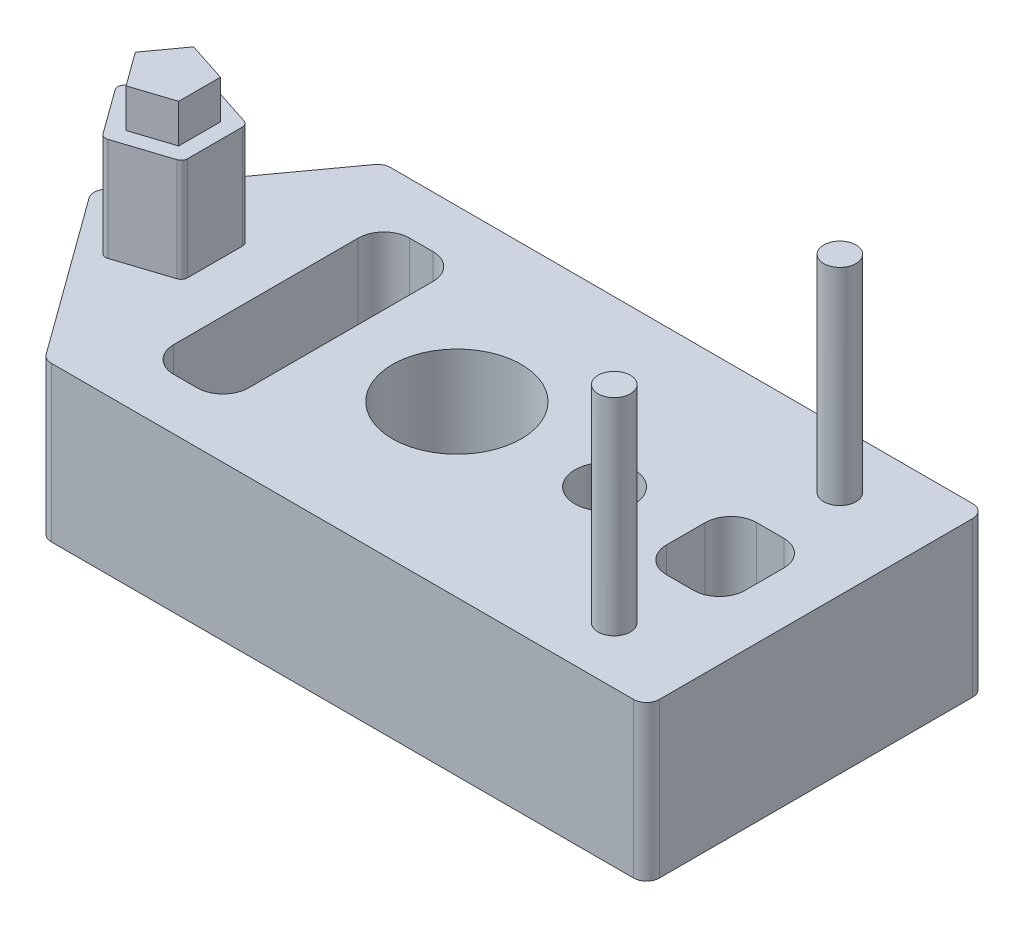
SolidWorks part; units mm, degrees
ref_plane "Front Plane" through (0, 0, 0) normal (0, 0, 1) x (1, 0, 0)
ref_plane "Top Plane" through (0, 0, 0) normal (0, 1, 0) x (1, 0, 0)
ref_plane "Right Plane" through (0, 0, 0) normal (1, 0, 0) x (0, 0, -1)
sketch "Sketch1" plane through (0, 0, 0) normal (0, 1, 0) x (1, 0, 0)
  line L0 (27.85, 13.15) -> (-18.2757, 13.15)
  line L1 (-18.2757, -13.15) -> (27.85, -13.15)
  line L2 (27.85, 13.15) -> (27.85, -13.15)
  line L3 (-11.15, 11.15) -> (25.85, 11.15) construction
  line L4 (-11.15, -11.15) -> (-11.15, 11.15) construction
  line L5 (25.85, 11.15) -> (25.85, -11.15) construction
  line L6 (25.85, -11.15) -> (-11.15, -11.15) construction
  line L7 (-18.2757, 13.15) -> (-18.8138, 13.15)
  line L8 (-25.1875, 0) -> (-23.1146, -2.8532) construction
  line L9 (-23.1146, -2.8532) -> (-19.7604, -1.7634) construction
  line L10 (-19.7604, -1.7634) -> (-19.7604, 1.7634) construction
  line L11 (-19.7604, 1.7634) -> (-23.1146, 2.8532) construction
  line L12 (-23.1146, 2.8532) -> (-25.1875, 0) construction
  line L13 (-18.8138, 13.15) -> (-28.3678, 0)
  line L14 (-18.2757, -13.15) -> (-18.8138, -13.15)
  line L15 (-18.8138, -13.15) -> (-28.3678, 0)
  line L16 (-22.1875, 0) -> (-17.1875, 0) construction
  circle A0 centre (-97.1875, 0) radius 80 construction
  circle A1 centre (-97.1875, 0) radius 81.5625 construction
  circle A2 centre (0, 0) radius 15.625 construction
  circle A4 centre (-22.1875, 0) radius 2.4271 construction
  point P10 (27.85, 0)
  point P14 (-11.15, 0)
  dimension "D1" = 160
  dimension "D2" = 163.125
  dimension "D3" = 31.25
  dimension "D9" = 3
  dimension "D4" = 11.15
  dimension "D5" = 22.3
  dimension "D6" = 37
  dimension "D7" = 2
  dimension "D8" = 2
  dimension "D10" = 5
  dimension "D11" = 5
extrude "Boss-Extrude2" add sketch "Sketch1" against normal blind 12
sketch "Sketch3" plane through (0, 0, 0) normal (0, 1, 0) x (1, 0, 0)
  line L0 (-11.15, 13.15) -> (-11.15, -13.15)
  line L1 (27.85, 13.15) -> (-18.8138, 13.15) construction
  line L2 (-18.8138, -13.15) -> (27.85, -13.15) construction
  circle A0 centre (0, 0) radius 5
  circle A1 centre (11.45, 0) radius 1.9 construction
  circle A2 centre (11.45, 0) radius 2.3
  circle A3 centre (0, 0) radius 2.7 construction
  dimension "D1" = 10
  dimension "D4" = 3.8
  dimension "D5" = 0.4
  dimension "D6" = 5.4
  dimension "D2" = 11.15
  dimension "D3" = 22.6
extrude "Cut-Extrude1" cut sketch "Sketch3" against normal through all contours A0 | A2
sketch "Sketch5" plane through (0, 0, 0) normal (0, 1, 0) x (1, 0, 0)
  line L0 (-11.15, -13.15) -> (-11.15, 13.15) construction
  line L1 (-18.8138, -13.15) -> (27.85, -13.15) construction
  line L2 (27.85, 13.15) -> (-18.8138, 13.15) construction
  line L3 (20.95, 8.75) -> (20.95, -8.75) construction
  circle A0 centre (20.95, -8.75) radius 1.25
  circle A1 centre (20.95, 8.75) radius 1.25
  point P11 (20.95, 0)
  dimension "D4" = 2.5
  dimension "D1" = 11.15
  dimension "D2" = 32.1
  dimension "D3" = 17.5
extrude "Boss-Extrude3" add sketch "Sketch5" along normal blind 16
sketch "Sketch6" plane through (0, 0, 0) normal (0, 1, 0) x (1, 0, 0)
  line L0 (-22.1875, 0) -> (-17.1875, 0) construction
  line L1 (-25.1875, 0) -> (-23.1146, -2.8532) construction
  line L2 (-23.1146, -2.8532) -> (-19.7604, -1.7634) construction
  line L3 (-19.7604, -1.7634) -> (-19.7604, 1.7634) construction
  line L4 (-19.7604, 1.7634) -> (-23.1146, 2.8532) construction
  line L5 (-23.1146, 2.8532) -> (-25.1875, 0) construction
  line L7 (-26.4236, 0) -> (-23.4965, -4.0287)
  line L8 (-23.4965, -4.0287) -> (-18.7604, -2.4899)
  line L9 (-18.7604, -2.4899) -> (-18.7604, 2.4899)
  line L10 (-18.7604, 2.4899) -> (-23.4965, 4.0287)
  line L11 (-23.4965, 4.0287) -> (-26.4236, 0)
  circle A0 centre (0, 0) radius 15.625 construction
  circle A1 centre (-97.1875, 0) radius 81.5625 construction
  circle A2 centre (-97.1875, 0) radius 80 construction
  circle A3 centre (-22.1875, 0) radius 2.4271 construction
  circle A4 centre (-97.1875, 0) radius 65 construction
  circle A5 centre (-22.1875, 0) radius 3.4271 construction
  dimension "D1" = 163.125
  dimension "D2" = 31.25
  dimension "D3" = 160
  dimension "D6" = 130
  dimension "D4" = 3
  dimension "D5" = 5
  dimension "D7" = 1
extrude "Boss-Extrude4" add sketch "Sketch6" along normal blind 11
sketch "Sketch7" plane through (0, 11, 0) normal (0, 1, 0) x (1, 0, 0)
  line L1 (-25.1875, 0) -> (-23.1146, -2.8532) construction
  line L2 (-23.1146, -2.8532) -> (-19.7604, -1.7634) construction
  line L3 (-19.7604, -1.7634) -> (-19.7604, 1.7634) construction
  line L4 (-19.7604, 1.7634) -> (-23.1146, 2.8532) construction
  line L5 (-23.1146, 2.8532) -> (-25.1875, 0) construction
  line L6 (-24.9403, 0) -> (-23.0382, -2.6181)
  line L7 (-23.0382, -2.6181) -> (-19.9604, -1.618)
  line L8 (-19.9604, -1.618) -> (-19.9604, 1.618)
  line L9 (-19.9604, 1.618) -> (-23.0382, 2.6181)
  line L10 (-23.0382, 2.6181) -> (-24.9403, 0)
  line L11 (-26.4236, 0) -> (-23.4965, -4.0287)
  line L12 (-23.4965, -4.0287) -> (-18.7604, -2.4899)
  line L13 (-18.7604, -2.4899) -> (-18.7604, 2.4899)
  line L14 (-18.7604, 2.4899) -> (-23.4965, 4.0287)
  line L15 (-23.4965, 4.0287) -> (-26.4236, 0)
  circle A0 centre (-22.1875, 0) radius 2.4271 construction
  circle A2 centre (-22.1875, 0) radius 2.2271 construction
  circle A3 centre (-22.1875, 0) radius 3.4271 construction
  dimension "D1" = 3
  dimension "D2" = 0.2
extrude "Cut-Extrude2" cut sketch "Sketch7" against normal blind 3
fillet "Fillet1" radius 0.5 5 edges at (-18.7604, 4, -2.4899) (-23.4965, 4, -4.0287) (-18.7604, 4, 2.4899) (-23.4965, 4, 4.0287) (-26.4236, 4, 0)
sketch "Sketch9" plane through (0, 0, 0) normal (0, 1, 0) x (1, 0, 0)
  line L0 (-18.8138, 13.15) -> (-18.8138, -13.15) construction
  line L1 (-14.8138, 9.15) -> (-14.8138, -9.15)
  line L2 (-14.8138, -9.15) -> (-9, -9.15)
  line L3 (-9, -9.15) -> (-9, 9.15)
  line L4 (-9, 9.15) -> (-14.8138, 9.15)
  line L5 (-9, 0) -> (-5, 0) construction
  line L6 (-18.8138, -13.15) -> (27.85, -13.15) construction
  line L7 (17.75, 3.5) -> (23.85, 3.5)
  line L8 (23.85, 3.5) -> (23.85, -3.5)
  line L9 (23.85, -3.5) -> (17.75, -3.5)
  line L10 (17.75, -3.5) -> (17.75, 3.5)
  line L11 (27.85, -13.15) -> (27.85, 13.15) construction
  line L12 (13.75, 0) -> (17.75, 0) construction
  line L13 (20.95, 7.5) -> (20.95, 3.5) construction
  line L14 (20.95, 8.75) -> (20.95, 3.5) construction
  circle A0 centre (0, 0) radius 5 construction
  circle A1 centre (11.45, 0) radius 2.3 construction
  circle A2 centre (20.95, 8.75) radius 1.25 construction
  point P2 (-18.8138, 0)
  point P9 (-14.8138, 0)
  point P21 (17.75, 0)
  dimension "D1" = 4
  dimension "D2" = 4
  dimension "D3" = 4
  dimension "D4" = 4
  dimension "D5" = 4
  dimension "D6" = 4
fillet "Fillet2" radius 1 5 edges at (-18.8138, -6, -13.15) (27.85, -6, -13.15) (27.85, -6, 13.15) (-18.8138, -6, 13.15) (-28.3678, -6, 0)
extrude "Cut-Extrude3" cut sketch "Sketch9" against normal through all
fillet "Fillet3" radius 2 8 edges at (17.75, -6, -3.5) (23.85, -6, -3.5) (23.85, -6, 3.5) (17.75, -6, 3.5) (-14.8138, -6, 9.15) (-9, -6, 9.15) (-14.8138, -6, -9.15) (-9, -6, -9.15)
